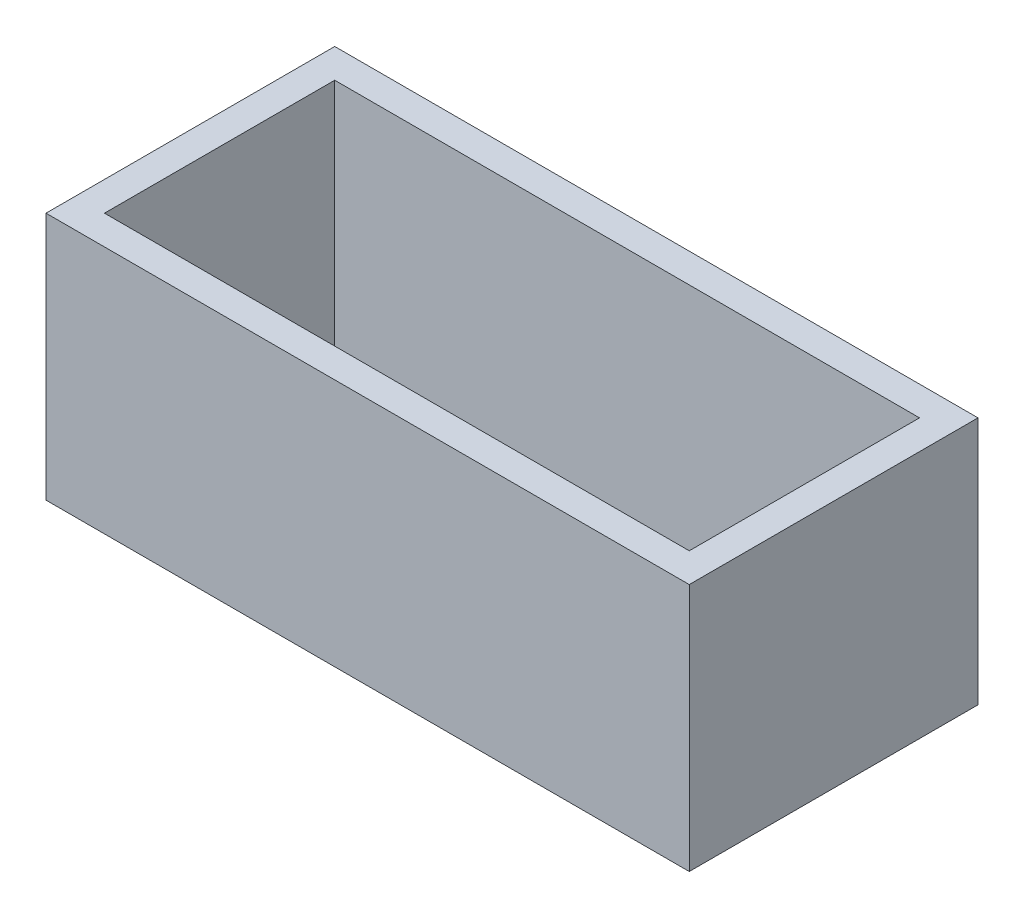
SolidWorks part; units mm, degrees
ref_plane "Front Plane" through (0, 0, 0) normal (0, 0, 1) x (1, 0, 0)
ref_plane "Top Plane" through (0, 0, 0) normal (0, 1, 0) x (1, 0, 0)
ref_plane "Right Plane" through (0, 0, 0) normal (1, 0, 0) x (0, 0, -1)
sketch "Sketch1" plane through (0, 0, 0) normal (0, 1, 0) x (1, 0, 0)
  line L0 (22, 9.875) -> (-22, 9.875)
  line L1 (20, -7.875) -> (-20, -7.875)
  line L2 (20, -7.875) -> (20, 7.875)
  line L3 (20, 7.875) -> (-20, 7.875)
  line L4 (-20, -7.875) -> (-20, 7.875)
  line L5 (20, -7.875) -> (-20, 7.875) construction
  line L6 (20, 7.875) -> (-20, -7.875) construction
  line L7 (-22, -9.875) -> (-22, 9.875)
  line L8 (22, -9.875) -> (-22, -9.875)
  line L9 (22, -9.875) -> (22, 9.875)
  point P0 (0, 0)
  dimension "D1" = 15.75
  dimension "D2" = 40
  dimension "D3" = 2
extrude "Boss-Extrude1" add sketch "Sketch1" along normal blind 17
